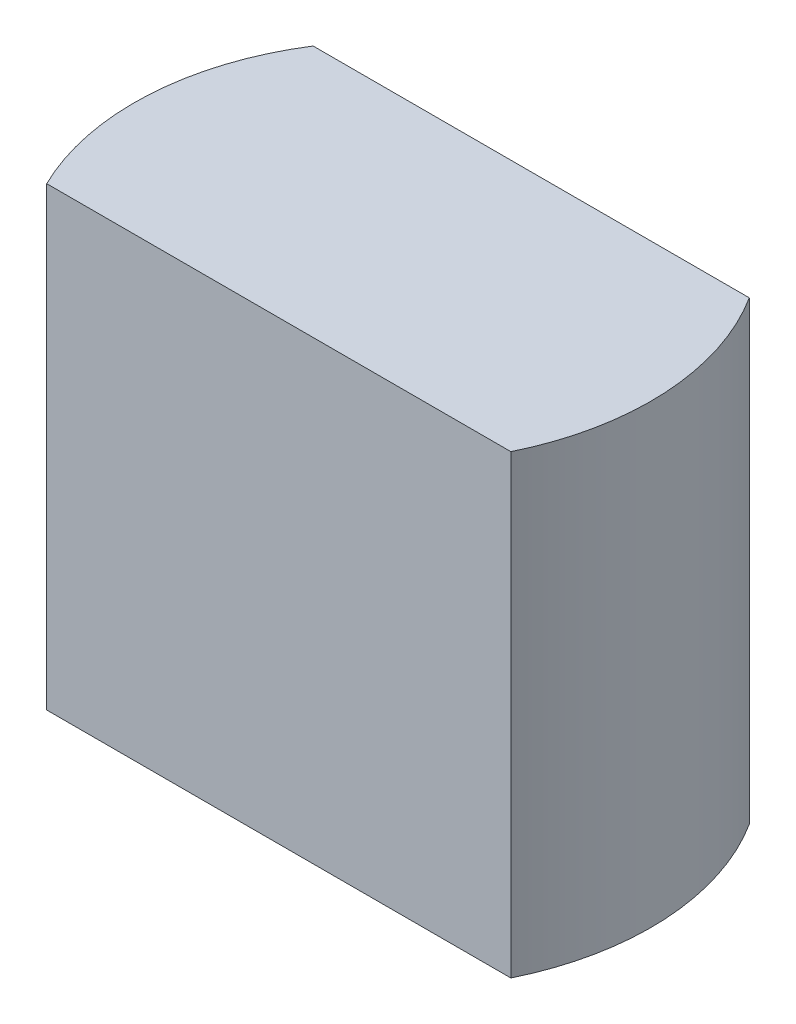
SolidWorks part; units mm, degrees
ref_plane "Front Plane" through (0, 0, 0) normal (0, 0, 1) x (1, 0, 0)
ref_plane "Top Plane" through (0, 0, 0) normal (0, 1, 0) x (1, 0, 0)
ref_plane "Right Plane" through (0, 0, 0) normal (1, 0, 0) x (0, 0, -1)
sketch "Sketch1" plane through (0, 0, 0) normal (0, 1, 0) x (1, 0, 0)
  circle A0 centre (0, 0) radius 4.5
extrude "Boss-Extrude1" add sketch "Sketch1" along normal blind 7.9371
sketch "Sketch2" plane through (0, 7.9371, 0) normal (0, 1, 0) x (1, 0, 0)
  line L1 (-4.6631, 2.415) -> (4.5928, 2.415)
  line L2 (-4.6631, 2.415) -> (-4.6631, 7.4381)
  line L3 (-4.6631, 7.4381) -> (4.5928, 7.4381)
  line L4 (4.5928, 2.415) -> (4.5928, 7.4381)
extrude "Cut-Extrude1" cut sketch "Sketch2" against normal up to surface (7.9371 mm away) up to face at (0, 0, 4.5)
sketch "Sketch3" plane through (0, 7.9371, 0) normal (0, 1, 0) x (1, 0, 0)
  line L1 (-4.5419, -1.9804) -> (5.0688, -1.9804)
  line L2 (-4.5419, -1.9804) -> (-4.5419, -5.5212)
  line L3 (-4.5419, -5.5212) -> (5.0688, -5.5212)
  line L4 (5.0688, -1.9804) -> (5.0688, -5.5212)
extrude "Cut-Extrude2" cut sketch "Sketch3" against normal up to surface (7.9371 mm away) up to face at (0, 0, 1.0425)
